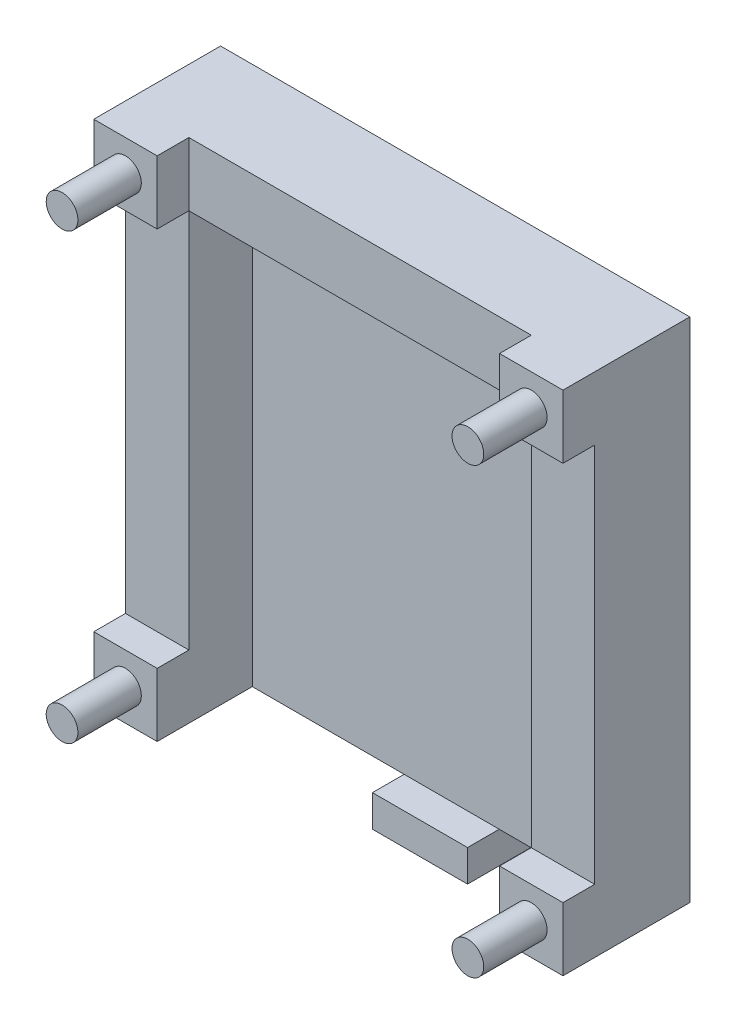
SolidWorks part; units mm, degrees
ref_plane "Alzado" through (0, 0, 0) normal (0, 0, 1) x (1, 0, 0)
ref_plane "Planta" through (0, 0, 0) normal (0, 1, 0) x (1, 0, 0)
ref_plane "Vista lateral" through (0, 0, 0) normal (1, 0, 0) x (0, 0, -1)
sketch "Croquis1" plane through (0, 0, 0) normal (0, 0, 1) x (1, 0, 0)
  line L0 (1.4005, 36.5086) -> (55.4005, 36.5086)
  line L1 (55.4005, 36.5086) -> (55.4005, -33.4914)
  line L2 (55.4005, -33.4914) -> (1.4005, -33.4914)
  line L3 (1.4005, -33.4914) -> (1.4005, 36.5086)
  dimension "D1" = 54
  dimension "D2" = 70
extrude "Saliente-Extruir1" add sketch "Croquis1" along normal blind 5
sketch "Croquis2" plane through (0, 0, 5) normal (0, 0, 1) x (1, 0, 0)
  line L0 (1.4005, 36.5086) -> (-8.0995, 36.5086)
  line L1 (55.4005, 36.5086) -> (1.4005, 36.5086) construction
  line L2 (55.4005, 36.5086) -> (1.4005, 36.5086)
  line L3 (1.4005, 36.5086) -> (1.4005, -33.4914)
  line L4 (1.4005, -33.4914) -> (55.4005, -33.4914) construction
  line L5 (1.4005, -33.4914) -> (-8.0995, -33.4914)
  line L6 (-8.0995, -33.4914) -> (-8.0995, 36.5086)
  line L7 (1.4005, 36.5086) -> (-8.0995, 36.5086)
sketch "Croquis4" plane through (0, 0, 0) normal (0, 0, -1) x (-1, 0, 0)
  line L0 (-55.4005, 36.5086) -> (-55.4005, 46.5086)
  line L1 (-55.4005, 46.5086) -> (-1.4005, 46.5086)
  line L2 (-1.4005, 46.5086) -> (-1.4005, 36.5086)
  line L3 (-1.4005, 36.5086) -> (-55.4005, 36.5086)
  dimension "D1" = 10
extrude "Saliente-Extruir5" add sketch "Croquis4" against normal blind 15
sketch "Croquis5" plane through (0, 0, 0) normal (0, 0, -1) x (-1, 0, 0)
  line L0 (-55.4005, 46.5086) -> (-65.4005, 46.5086)
  line L1 (-65.4005, 46.5086) -> (-65.4005, 36.5086)
  line L2 (-65.4005, 36.5086) -> (-55.4005, 36.5086)
  line L3 (-55.4005, 36.5086) -> (-55.4005, 46.5086)
  line L4 (-55.4005, 46.5086) -> (-28.4005, 46.5086)
  line L5 (-1.4005, 46.5086) -> (-55.4005, 46.5086) construction
  line L6 (-28.4005, 46.5086) -> (-28.4005, 24.5969)
  line L7 (-55.4005, -33.4914) -> (-65.4005, -33.4914)
  line L8 (-65.4005, -33.4914) -> (-65.4005, -23.4914)
  line L9 (-65.4005, -23.4914) -> (-55.4005, -23.4914)
  line L10 (-55.4005, -33.4914) -> (-55.4005, 46.5086) construction
  line L11 (-55.4005, -23.4914) -> (-55.4005, -33.4914)
  line L12 (-55.4005, -33.4914) -> (-55.597, -33.6261)
  line L13 (-1.4005, -23.4914) -> (-1.4005, -33.4914)
  line L14 (8.5995, -23.4914) -> (-1.4005, -23.4914)
  line L15 (8.5995, -33.4914) -> (8.5995, -23.4914)
  line L16 (-1.4005, -33.4914) -> (8.5995, -33.4914)
  line L17 (-1.4005, 36.5086) -> (-1.4005, 46.5086)
  line L18 (8.5995, 36.5086) -> (-1.4005, 36.5086)
  line L19 (8.5995, 46.5086) -> (8.5995, 36.5086)
  line L20 (-1.4005, 46.5086) -> (8.5995, 46.5086)
  line L21 (-1.4005, -33.4914) -> (-1.2041, -33.6261)
  line M1 (-1.4005, -33.4914) -> (-1.4005, 46.5086)
  line M3 (-55.4005, 46.5086) -> (-55.4005, -33.4914)
extrude "Saliente-Extruir6" add sketch "Croquis5" against normal blind 20 contours L1 L2 L0 M3 | L9 L8 L7 M3 | L16 L15 L14 M1 | L20 L18 L19 M1
sketch "Croquis6" plane through (0, 0, 0) normal (0, 0, -1) x (-1, 0, 0)
  line L1 (8.5995, -33.4914) -> (-65.4005, -33.4914) construction
  line L3 (-40.349, -38.4914) -> (-40.349, -33.4914)
  line L4 (-40.349, -33.4914) -> (-25.349, -33.4914)
  line L5 (-25.349, -33.4914) -> (-25.349, -38.4914)
  line L6 (-25.349, -38.4914) -> (-40.349, -38.4914)
  dimension "D1" = 5
  dimension "D4" = 15
extrude "Saliente-Extruir7" add sketch "Croquis6" against normal blind 10 separate body
sketch "Croquis8" plane through (0, 0, 0) normal (0, 0, -1) x (-1, 0, 0)
  line L0 (-65.4005, 36.5086) -> (-65.4005, -23.4914)
  line L1 (-65.4005, -23.4914) -> (-55.4005, -23.4914)
  line L2 (-55.4005, -23.4914) -> (-55.4005, 36.5086)
  line L3 (-55.4005, 36.5086) -> (-65.4005, 36.5086)
  line L4 (-28.4005, 46.5086) -> (-28.4005, 34.2655)
  line L5 (8.5995, 46.5086) -> (-65.4005, 46.5086) construction
  line L6 (-1.4005, 36.5086) -> (8.5995, 36.5086)
  line L7 (-1.4005, -23.4914) -> (-1.4005, 36.5086)
  line L8 (8.5995, -23.4914) -> (-1.4005, -23.4914)
  line L9 (8.5995, 36.5086) -> (8.5995, -23.4914)
  line M1 (-1.4005, -23.4914) -> (-1.4005, 36.5086)
  line M2 (-1.4005, 36.5086) -> (8.5995, 36.5086)
  line M6 (-65.4005, 36.5086) -> (-55.4005, 36.5086)
  line M7 (-55.4005, 36.5086) -> (-55.4005, -23.4914)
  line M8 (-55.4005, -23.4914) -> (-65.4005, -23.4914)
  line M12 (8.5995, -23.4914) -> (-1.4005, -23.4914)
extrude "Saliente-Extruir9" add sketch "Croquis8" against normal blind 15 contours L0 M6 M8 M7 | L9 M2 M1 M12
sketch "Croquis9" plane through (0, 0, 20) normal (0, 0, 1) x (1, 0, 0)
  line L0 (-8.5995, 46.5086) -> (-8.5995, 36.5086)
  line L1 (-8.5995, 46.5086) -> (-8.5995, 36.5086) construction
  line L2 (-8.5995, 41.5086) -> (1.4005, 41.5086)
  line L3 (1.4005, 36.5086) -> (1.4005, 46.5086) construction
  line L4 (-8.5995, 46.5086) -> (-8.5995, 6.5086)
  line L5 (-8.5995, 36.5086) -> (-8.5995, -23.4914) construction
  line L6 (-8.5995, 6.5086) -> (65.4005, 6.5086)
  line L7 (65.4005, 36.5086) -> (65.4005, -23.4914) construction
  line L8 (65.4005, 6.5086) -> (28.4005, 6.5086)
  line L9 (28.4005, 6.5086) -> (28.4005, 19.0549)
  circle A0 centre (-3.5995, 41.5086) radius 2.5
  circle A1 centre (60.4005, 41.5086) radius 2.5
  circle A2 centre (60.4005, -28.4914) radius 2.5
  circle A3 centre (-3.5995, -28.4914) radius 2.5
  dimension "D1" = 5
extrude "Saliente-Extruir10" add sketch "Croquis9" along normal blind 10 contours L2 A0 | L2 A0 | A1 | A2 | A3
